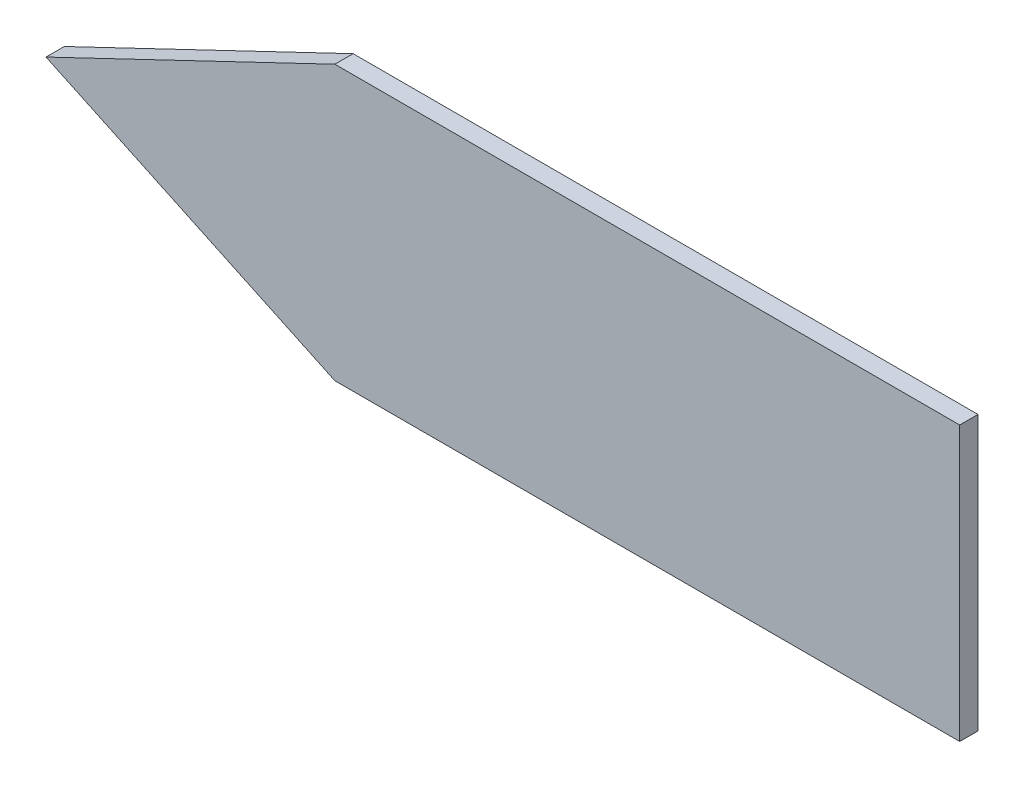
SolidWorks part; units mm, degrees
ref_plane "Plano frontal" through (0, 0, 0) normal (0, 0, 1) x (1, 0, 0)
ref_plane "Plano superior" through (0, 0, 0) normal (0, 1, 0) x (1, 0, 0)
ref_plane "Plano direito" through (0, 0, 0) normal (1, 0, 0) x (0, 0, -1)
sketch "Esboço1" plane through (0, 0, 0) normal (0, 0, 1) x (1, 0, 0)
  line L0 (15.8069, 0) -> (0, 0) construction
  line L2 (15.8069, -7.4369) -> (50, -7.4369)
  line L3 (15.8069, 7.5631) -> (50, 7.5631)
  line L4 (50, -7.4369) -> (50, 7.5631)
  line L5 (0, 0) -> (15.8069, 7.5631)
  line L6 (0, 0) -> (15.8069, -7.4369)
  dimension "D1" = 15
  dimension "D2" = 50
extrude "Ressalto-extrusão1" add sketch "Esboço1" along normal blind 1
